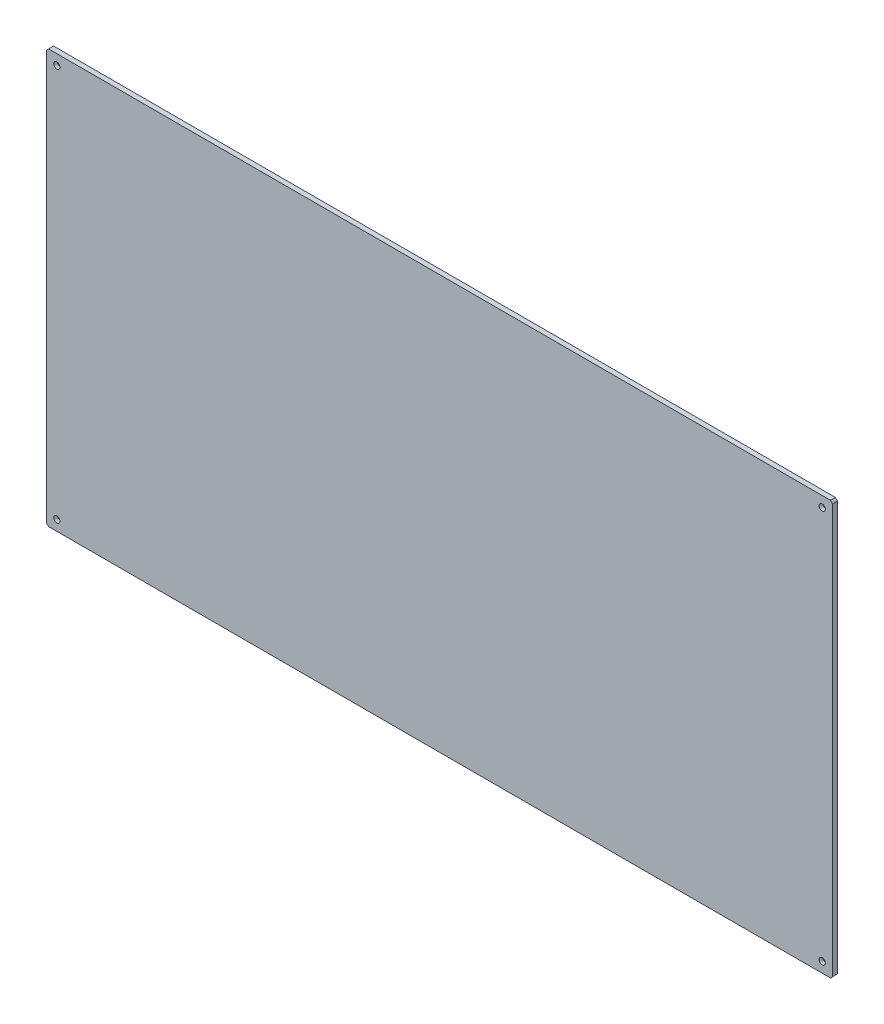
SolidWorks part; units mm, degrees
ref_plane "前视基准面" through (0, 0, 0) normal (0, 0, 1) x (1, 0, 0)
ref_plane "上视基准面" through (0, 0, 0) normal (0, 1, 0) x (1, 0, 0)
ref_plane "右视基准面" through (0, 0, 0) normal (1, 0, 0) x (0, 0, -1)
sketch "草图1" plane through (0, 0, 0) normal (0, 0, 1) x (1, 0, 0)
  line L1 (950, -500) -> (-950, -500)
  line L2 (950, -500) -> (950, 500)
  line L3 (950, 500) -> (-950, 500)
  line L4 (-950, -500) -> (-950, 500)
  line L5 (950, -500) -> (-950, 500) construction
  line L6 (950, 500) -> (-950, -500) construction
  point P0 (0, 0)
  dimension "D1" = 1900
  dimension "D2" = 1000
extrude "凸台-拉伸1" add sketch "草图1" along normal mid plane 12
hole_wizard "打孔尺寸(%根据)内六角圆柱头螺钉的类型1" positions "草图3" profile "草图2" counterbore size "M8" standard "GB" end condition through all
sketch "草图3" plane through (0, 0, 6) normal (0, 0, 1) x (1, 0, 0)
  line L0 (950, 500) -> (-950, 500) construction
  line L1 (-950, 500) -> (-950, -500) construction
  line L2 (950, -500) -> (950, 500) construction
  line L3 (-950, -500) -> (950, -500) construction
  point P0 (925, 475)
  point P2 (925, -475)
  point P4 (-925, -475)
  point P6 (-925, 475)
  dimension "D1" = 25
  dimension "D2" = 25
  dimension "D3" = 25
  dimension "D4" = 25
  dimension "D5" = 25
  dimension "D6" = 25
  dimension "D7" = 25
  dimension "D8" = 25
sketch "草图2" plane through (925, 475, 6) normal (1, 0, 0) x (0, -1, 0)
  line L0 (0, 0) -> (0, 12)
  line L1 (0, 12) -> (4.5, 12)
  line L3 (4.5, 12) -> (4.5, 9)
  line L4 (4.5, 9) -> (7.5, 9)
  line L5 (7.5, 9) -> (7.5, 0)
  line L7 (7.5, 0) -> (0, 0)
  line L11 (0, -6.35) -> (0, 107.95) construction
  dimension "通孔孔直径" = 9
  dimension "通孔孔深度" = 12
  dimension "柱形沉头孔直径" = 15
  dimension "柱形沉头孔深度" = 9
chamfer "倒角1" distance 5 angle 45 4 edges at (-950, 500, 0) (950, 500, 0) (-950, -500, 0) (950, -500, 0)
